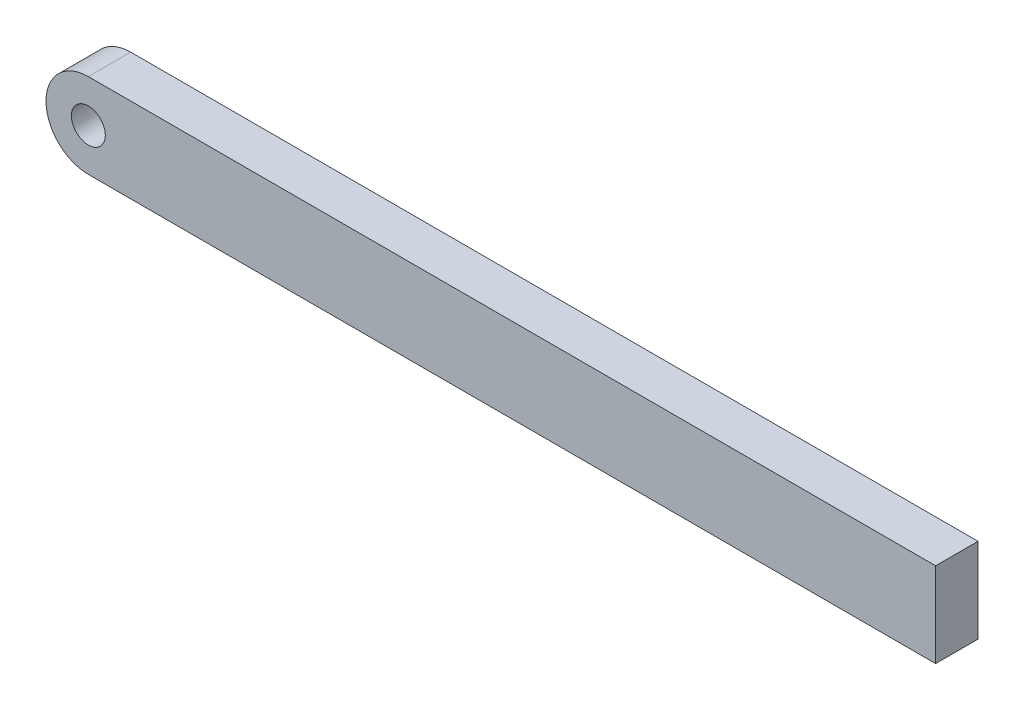
SolidWorks part; units mm, degrees
ref_plane "Front" through (0, 0, 0) normal (0, 0, 1) x (1, 0, 0)
ref_plane "Top" through (0, 0, 0) normal (0, 1, 0) x (1, 0, 0)
ref_plane "Right" through (0, 0, 0) normal (1, 0, 0) x (0, 0, -1)
sketch "草图1" plane through (0, 0, 0) normal (0, 0, 1) x (1, 0, 0)
  line L1 (0, 50) -> (1000, 50)
  line L3 (0, -50) -> (1000, -50)
  line L4 (1000, 50) -> (1000, -50)
  arc A0 (0, 50) -> (0, -50) centre (0, 0) ccw
  dimension "D1" = 100
  dimension "D2" = 1000
extrude "凸台-拉伸1" add sketch "草图1" along normal blind 50
sketch "草图2" plane through (0, 0, 50) normal (0, 0, 1) x (1, 0, 0)
  circle A0 centre (0, 0) radius 20
  dimension "D1" = 40
extrude "切除-拉伸1" cut sketch "草图2" against normal blind 30
